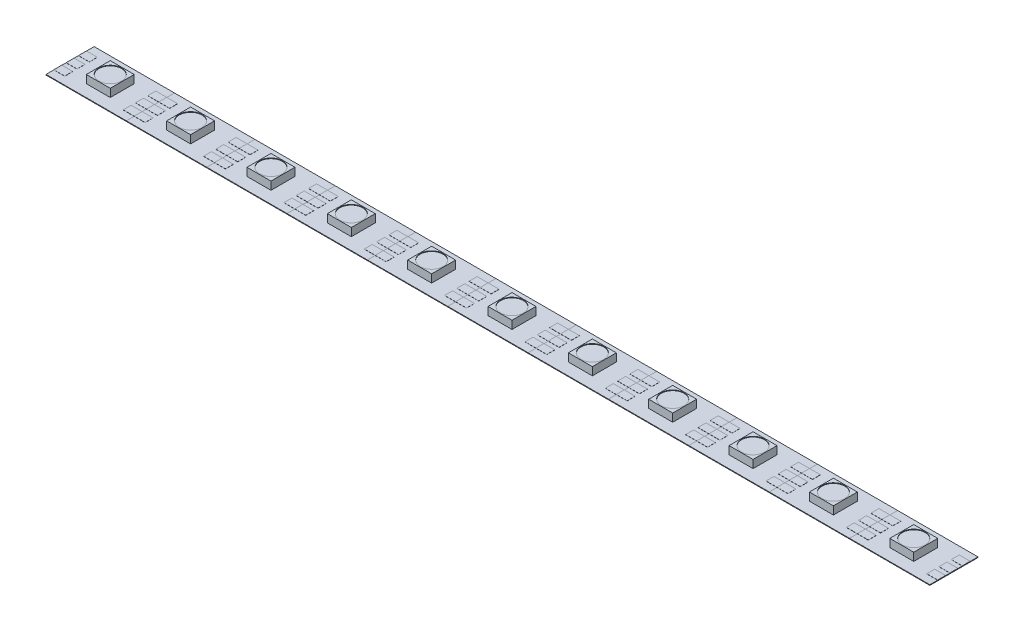
SolidWorks part; units mm, degrees
ref_plane "Front Plane" through (0, 0, 0) normal (0, 0, 1) x (1, 0, 0)
ref_plane "Top Plane" through (0, 0, 0) normal (0, 1, 0) x (1, 0, 0)
ref_plane "Right Plane" through (0, 0, 0) normal (1, 0, 0) x (0, 0, -1)
sketch "Sketch1" plane through (0, 0, 0) normal (0, 1, 0) x (1, 0, 0)
  line L0 (-8.3058, 4.9784) -> (8.3058, -4.9784) construction
  line L1 (-8.3058, 4.9784) -> (8.3058, 4.9784)
  line L2 (-8.3058, 4.9784) -> (-8.3058, -4.9784)
  line L3 (-8.3058, -4.9784) -> (8.3058, -4.9784)
  line L4 (8.3058, 4.9784) -> (8.3058, -4.9784)
  dimension "D1" = 9.9568
  dimension "D2" = 16.6116
extrude "Boss-Extrude1" add sketch "Sketch1" along normal blind 0.127
sketch "Sketch3" plane through (0, 0.127, 0) normal (0, 1, 0) x (1, 0, 0)
  line L0 (-8.3058, 4.9784) -> (8.3058, -4.9784) construction
  line L1 (-2.4765, 2.4765) -> (2.4765, -2.4765) construction
  line L2 (-2.4765, 2.4765) -> (2.4765, 2.4765)
  line L3 (-2.4765, 2.4765) -> (-2.4765, -2.4765)
  line L4 (-2.4765, -2.4765) -> (2.4765, -2.4765)
  line L5 (2.4765, 2.4765) -> (2.4765, -2.4765)
  dimension "D1" = 4.953
extrude "Boss-Extrude3" add sketch "Sketch3" along normal blind 1.651
sketch "Sketch4" plane through (0, 0.127, 0) normal (0, 1, 0) x (1, 0, 0)
  line L0 (-8.3058, 0) -> (8.3058, 0) construction
  line L1 (-8.3058, 4.9784) -> (-8.3058, -4.9784) construction
  line L2 (8.3058, -4.9784) -> (8.3058, 4.9784) construction
  line L3 (-6.047, 0) -> (-8.3058, 0) construction
  line L4 (-8.3058, 0.8255) -> (-6.047, 0.8255)
  line L5 (-8.3058, 0.8255) -> (-8.3058, -0.8255)
  line L6 (-8.3058, -0.8255) -> (-6.047, -0.8255)
  line L7 (-6.047, 0.8255) -> (-6.047, -0.8255)
  line L8 (-8.3058, 3.3655) -> (-6.047, 3.3655)
  line L9 (-6.047, 3.3655) -> (-6.047, 1.7145)
  line L10 (-8.3058, 1.7145) -> (-6.047, 1.7145)
  line L11 (-8.3058, 3.3655) -> (-8.3058, 1.7145)
  line L12 (-6.047, -3.3655) -> (-6.047, -1.7145)
  line L13 (-8.3058, -1.7145) -> (-6.047, -1.7145)
  line L14 (-8.3058, -3.3655) -> (-8.3058, -1.7145)
  line L15 (-8.3058, -3.3655) -> (-6.047, -3.3655)
  line L16 (0, 0) -> (0, -4.9784) construction
  line L17 (-8.3058, -4.9784) -> (8.3058, -4.9784) construction
  line L18 (8.3058, -3.3655) -> (8.3058, -1.7145)
  line L19 (8.3058, -3.3655) -> (6.047, -3.3655)
  line L20 (6.047, -3.3655) -> (6.047, -1.7145)
  line L21 (8.3058, -1.7145) -> (6.047, -1.7145)
  line L22 (8.3058, 0.8255) -> (8.3058, -0.8255)
  line L23 (8.3058, -0.8255) -> (6.047, -0.8255)
  line L24 (6.047, 0.8255) -> (6.047, -0.8255)
  line L25 (8.3058, 0.8255) -> (6.047, 0.8255)
  line L26 (8.3058, 1.7145) -> (6.047, 1.7145)
  line L27 (6.047, 3.3655) -> (6.047, 1.7145)
  line L28 (8.3058, 3.3655) -> (8.3058, 1.7145)
  line L29 (8.3058, 3.3655) -> (6.047, 3.3655)
  dimension "D1" = 1.651
  dimension "D2" = 2
extrude "Boss-Extrude4" add sketch "Sketch4" along normal blind 0.0254
sketch "Sketch5" plane through (0, 1.778, 0) normal (0, 1, 0) x (1, 0, 0)
  circle A0 centre (0, 0) radius 2.3483
extrude "Cut-Extrude1" cut sketch "Sketch5" against normal blind 0.127
pattern_linear "LPattern1" count 11 spacing 16.6116 along (1, 0, 0) of "Boss-Extrude3", "Boss-Extrude4", "Cut-Extrude1", "Boss-Extrude1"
